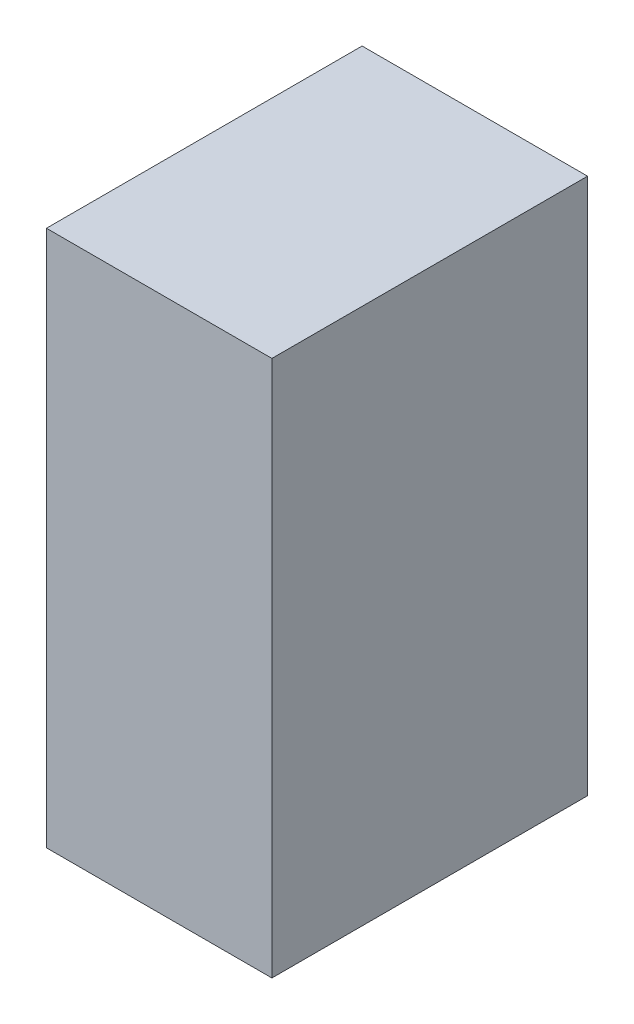
SolidWorks part; units mm, degrees
ref_plane "Front Plane" through (0, 0, 0) normal (0, 0, 1) x (1, 0, 0)
ref_plane "Top Plane" through (0, 0, 0) normal (0, 1, 0) x (1, 0, 0)
ref_plane "Right Plane" through (0, 0, 0) normal (1, 0, 0) x (0, 0, -1)
sketch "Sketch1" plane through (0, 0, 0) normal (0, 0, 1) x (1, 0, 0)
  line L1 (-12.5429, 625) -> (12.4571, 625)
  line L2 (-12.5429, 625) -> (-12.5429, 565.5024)
  line L3 (-12.5429, 565.5024) -> (12.4571, 565.5024)
  line L4 (12.4571, 625) -> (12.4571, 565.5024)
extrude "Boss-Extrude1" add sketch "Sketch1" along normal blind 35
